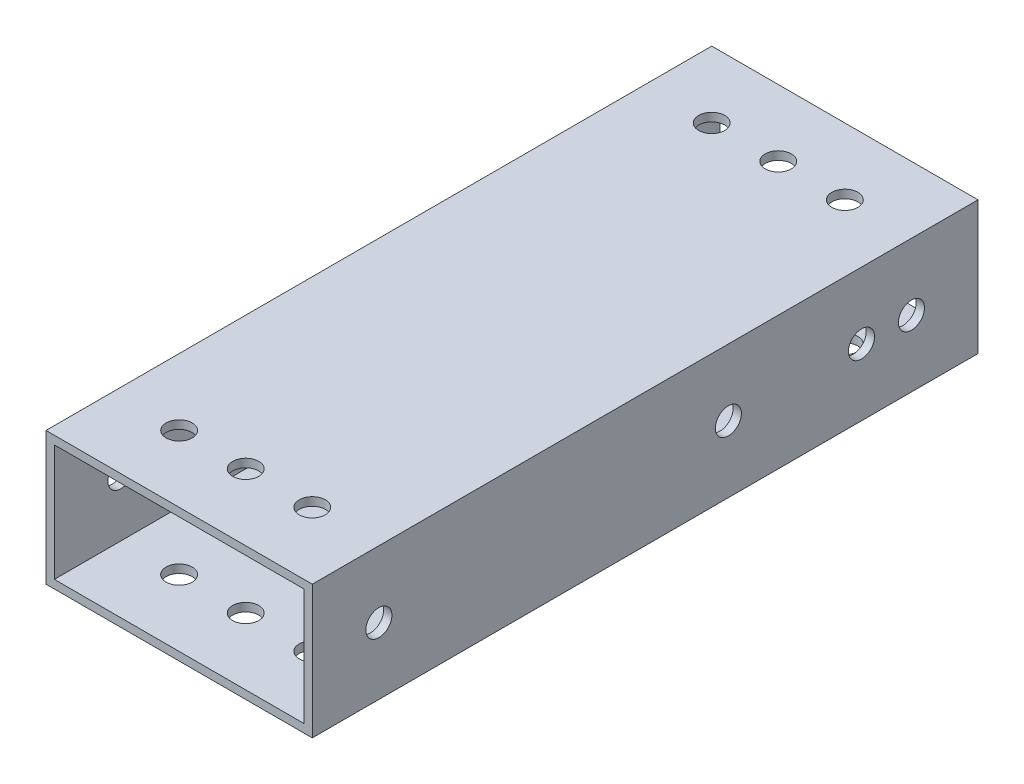
SolidWorks part; units mm, degrees
material "6061-T6 (SS)"
ref_plane "Front Plane" through (0, 0, 0) normal (0, 0, 1) x (1, 0, 0)
ref_plane "Top Plane" through (0, 0, 0) normal (0, 1, 0) x (1, 0, 0)
ref_plane "Right Plane" through (0, 0, 0) normal (1, 0, 0) x (0, 0, -1)
sketch "Sketch1" plane through (0, 0, 0) normal (0, 0, 1) x (1, 0, 0)
  line L0 (-23.8125, 11.1125) -> (23.8125, 11.1125)
  line L1 (-25.4, -12.7) -> (25.4, -12.7)
  line L2 (-25.4, -12.7) -> (-25.4, 12.7)
  line L3 (-25.4, 12.7) -> (25.4, 12.7)
  line L4 (25.4, -12.7) -> (25.4, 12.7)
  line L5 (-25.4, -12.7) -> (25.4, 12.7) construction
  line L6 (-25.4, 12.7) -> (25.4, -12.7) construction
  line L7 (23.8125, -11.1125) -> (23.8125, 11.1125)
  line L8 (-23.8125, -11.1125) -> (23.8125, -11.1125)
  line L9 (-23.8125, -11.1125) -> (-23.8125, 11.1125)
  point P0 (0, 0)
  dimension "D1" = 50.8
  dimension "D2" = 25.4
  dimension "D3" = 1.5875
extrude "Boss-Extrude1" add sketch "Sketch1" along normal mid plane 127
sketch "Sketch2" plane through (0, 12.7, 0) normal (0, 1, 0) x (1, 0, 0)
  line L0 (25.4, 63.5) -> (-25.4, 63.5) construction
  line L1 (25.4, 0) -> (-25.4, 0) construction
  line L2 (25.4, -63.5) -> (25.4, 63.5) construction
  line L3 (-25.4, -63.5) -> (-25.4, 63.5) construction
  circle A0 centre (-12.7, 50.8) radius 2.4892
  circle A1 centre (0, 50.8) radius 2.4892
  circle A2 centre (12.7, 50.8) radius 2.4892
  circle A3 centre (12.7, -50.8) radius 2.4892
  circle A4 centre (0, -50.8) radius 2.4892
  circle A5 centre (-12.7, -50.8) radius 2.4892
  dimension "D4" = 4.9784
  dimension "D1" = 12.7
  dimension "D2" = 12.7
  dimension "D3" = 12.7
extrude "Cut-Extrude1" cut sketch "Sketch2" against normal through all
sketch "Sketch3" plane through (-25.4, 0, 0) normal (-1, 0, 0) x (0, 0, 1)
  line L0 (-63.5, 12.7) -> (-63.5, -12.7) construction
  line L1 (0, 12.7) -> (0, -12.7) construction
  line L2 (63.5, 12.7) -> (-63.5, 12.7) construction
  line L3 (63.5, -12.7) -> (-63.5, -12.7) construction
  circle A0 centre (-50.8, 0) radius 2.4892
  circle A1 centre (50.8, 0) radius 2.4892
  dimension "D1" = 4.9784
  dimension "D2" = 12.7
extrude "Cut-Extrude2" cut sketch "Sketch3" against normal through all
sketch "Sketch5" plane through (25.4, 0, 0) normal (1, 0, 0) x (0, 0, -1)
  line L0 (63.5, -12.7) -> (63.5, 12.7) construction
  circle A1 centre (41.275, 0) radius 2.4892
  circle A2 centre (15.875, 0) radius 2.4892
  dimension "D1" = 25.4
  dimension "D3" = 4.9784
  dimension "D4" = 22.225
extrude "Cut-Extrude3" cut sketch "Sketch5" against normal through all
